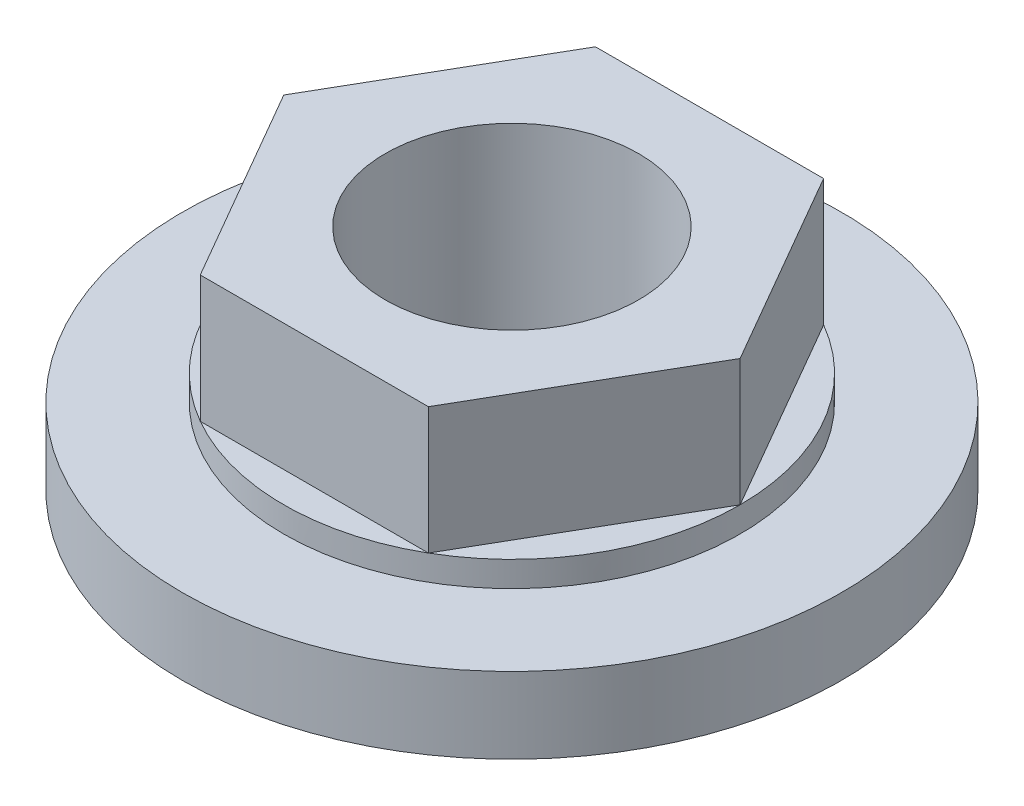
SolidWorks part; units mm, degrees
ref_plane "Front Plane" through (0, 0, 0) normal (0, 0, 1) x (1, 0, 0)
ref_plane "Top Plane" through (0, 0, 0) normal (0, 1, 0) x (1, 0, 0)
ref_plane "Right Plane" through (0, 0, 0) normal (1, 0, 0) x (0, 0, -1)
sketch "Sketch1" plane through (0, 0, 0) normal (0, 1, 0) x (1, 0, 0)
  circle A0 centre (0, 0) radius 6.5
  dimension "D1" = 13
extrude "Boss-Extrude1" add sketch "Sketch1" along normal blind 1.5
sketch "Sketch2" plane through (0, 1.5, 0) normal (0, 1, 0) x (1, 0, 0)
  circle A0 centre (0, 0) radius 4.5
  dimension "D1" = 9
extrude "Boss-Extrude2" add sketch "Sketch2" along normal blind 0.5
sketch "Sketch3" plane through (0, 2, 0) normal (0, 1, 0) x (1, 0, 0)
  line L1 (-4.5, 0) -> (-2.25, -3.8971)
  line L2 (-2.25, -3.8971) -> (2.25, -3.8971)
  line L3 (2.25, -3.8971) -> (4.5, 0)
  line L4 (4.5, 0) -> (2.25, 3.8971)
  line L5 (2.25, 3.8971) -> (-2.25, 3.8971)
  line L6 (-2.25, 3.8971) -> (-4.5, 0)
  circle A0 centre (0, 0) radius 3.8971 construction
  circle A1 centre (0, 0) radius 2.5
  dimension "D1" = 5
  dimension "D2" = 9
extrude "Boss-Extrude3" add sketch "Sketch3" along normal blind 2.5
sketch "Sketch4" plane through (0, 2, 0) normal (0, 1, 0) x (1, 0, 0)
  circle A1 centre (0, 0) radius 2.5
  circle A2 centre (0, 0) radius 2.5
  dimension "D1" = 0
extrude "Cut-Extrude1" cut sketch "Sketch4" against normal blind 3.5
